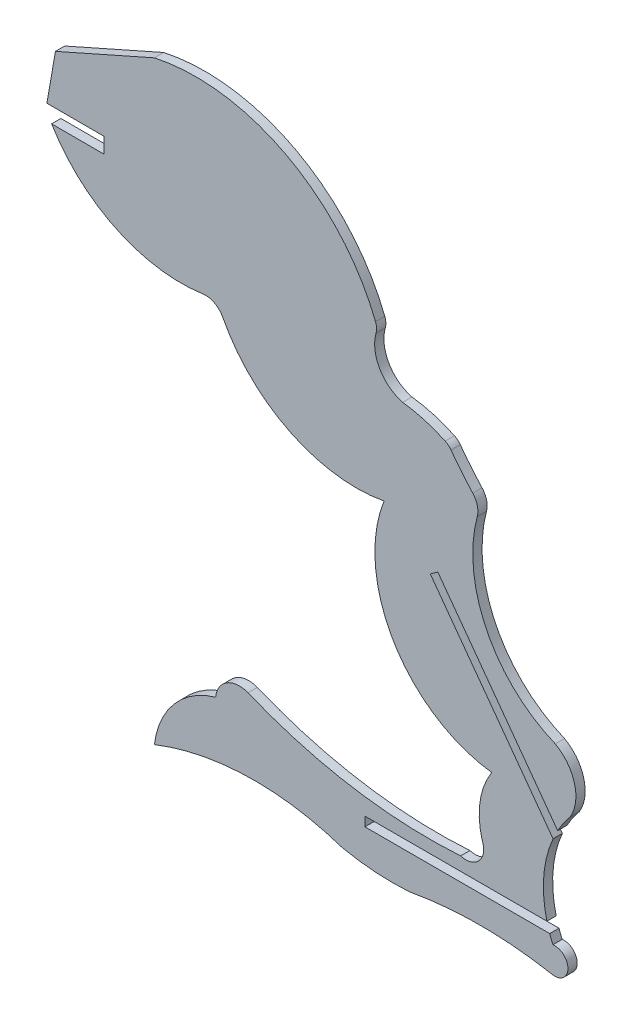
SolidWorks part; units mm, degrees
ref_plane "Front Plane" through (0, 0, 0) normal (0, 0, 1) x (1, 0, 0)
ref_plane "Top Plane" through (0, 0, 0) normal (0, 1, 0) x (1, 0, 0)
ref_plane "Right Plane" through (0, 0, 0) normal (1, 0, 0) x (0, 0, -1)
sketch "Sketch1" plane through (0, 0, 0) normal (0, 0, 1) x (1, 0, 0)
  line L0 (211.5237, 0) -> (211.5237, -2.54)
  line L1 (211.5237, -2.54) -> (202.9229, -2.5276)
  line L2 (211.5237, 0) -> (202.1482, 0.0136)
  line L3 (202.1482, 0.0136) -> (203.5536, 8.0958)
  line L4 (203.5536, 8.0958) -> (219.8014, 15.2991)
  line L5 (415.4863, -82.3745) -> (197.0188, -82.3745) construction
  line L6 (254.3833, -76.0279) -> (303.4816, -76.0279) construction
  line L7 (254.3833, -76.7899) -> (284.733, -76.7899)
  line L8 (254.3833, -75.2659) -> (284.2731, -75.2659)
  line L9 (254.3833, -76.7899) -> (254.3833, -75.2659)
  line L10 (288.0771, -65.5771) -> (265.735, -35.0069) construction
  line L11 (254.3833, -76.7899) -> (303.4816, -76.7899) construction
  line L12 (254.3833, -75.2659) -> (303.4816, -75.2659) construction
  line L13 (286.0434, -61.5031) -> (266.3502, -34.5573)
  line L14 (285.2799, -63.0412) -> (265.1198, -35.4565)
  line L16 (266.3502, -34.5573) -> (265.1198, -35.4565)
  line L17 (287.4619, -66.0268) -> (265.1198, -35.4565) construction
  line L18 (288.6923, -65.1275) -> (266.3502, -34.5573) construction
  arc A0 (256.1191, -4.0645) -> (256.2031, -5.6806) centre (253.7567, -4.9974) cw
  arc A1 (202.9229, -2.5276) -> (227.7462, -14.3004) centre (224.1751, 10.2265) ccw
  arc A2 (284.733, -76.7899) -> (285.2551, -78.1218) centre (302.4569, -70.6097) ccw
  arc A3 (268.523, -16.1311) -> (272.0917, -20.4757) centre (308.3511, 12.9458) ccw
  arc A4 (272.0917, -20.4757) -> (272.8261, -23.4413) centre (269.7571, -22.6275) cw
  arc A5 (272.8261, -23.4413) -> (285.6434, -49.3598) centre (294.0561, -29.071) ccw
  arc A6 (285.6434, -49.3598) -> (288.0771, -58.5452) centre (282.4126, -55.1309) cw
  arc A7 (288.0771, -58.5452) -> (286.0434, -61.5031) centre (302.4569, -70.6097) ccw
  arc A8 (285.2551, -78.1218) -> (284.9874, -82.3745) centre (285.5502, -80.2752) cw
  arc A9 (284.9874, -82.3745) -> (261.7071, -82.3745) centre (273.3472, -145.668) ccw
  arc A10 (261.7071, -82.3745) -> (250.7098, -81.6275) centre (258.9455, -41.7082) cw
  arc A11 (250.7098, -81.6275) -> (219.8014, -82.3745) centre (236.2796, -124.366) ccw
  arc A12 (219.8014, -82.3745) -> (229.8652, -70.6097) centre (233.6885, -84.067) cw
  arc A13 (229.8652, -70.6097) -> (235.1896, -67.3167) centre (233.7763, -70.9825) cw
  arc A14 (235.1896, -67.3167) -> (270.0981, -73.0624) centre (265.0075, 4.926) ccw
  arc A15 (270.0981, -73.0624) -> (273.6452, -69.0999) centre (270.9618, -70.2667) ccw
  arc A16 (273.6452, -69.0999) -> (275.203, -58.6567) centre (285.8128, -65.5771) cw
  arc A17 (275.203, -58.6567) -> (257.5211, -28.8798) centre (277.9767, -36.8713) cw
  arc A18 (257.5211, -28.8798) -> (231.0196, -15.9758) centre (252.9806, -4.5391) cw
  arc A19 (227.7462, -14.3004) -> (231.0196, -15.9758) centre (228.2036, -17.4423) cw
  arc A20 (285.2799, -63.0412) -> (284.2731, -75.2659) centre (302.4569, -70.6097) ccw
  arc A21 (219.8014, 15.2991) -> (256.1191, -4.0645) centre (226.5786, -15.7298) cw
  arc A22 (256.2031, -5.6806) -> (260.5798, -13.3092) centre (262.1466, -7.3405) ccw
  arc A23 (260.5798, -13.3092) -> (267.5588, -15.3333) centre (257.8002, -35.9375) cw
  arc A24 (267.5588, -15.3333) -> (268.523, -16.1311) centre (266.4716, -17.6288) cw
  dimension "D1" = 0.762
  dimension "D3" = 3.175
  dimension "D4" = 3.175
  dimension "D7" = 2.54
  dimension "D2" = 0.762
  dimension "D5" = 0.762
  dimension "D6" = 0.762
extrude "Boss-Extrude1" add sketch "Sketch1" along normal blind 1.524
